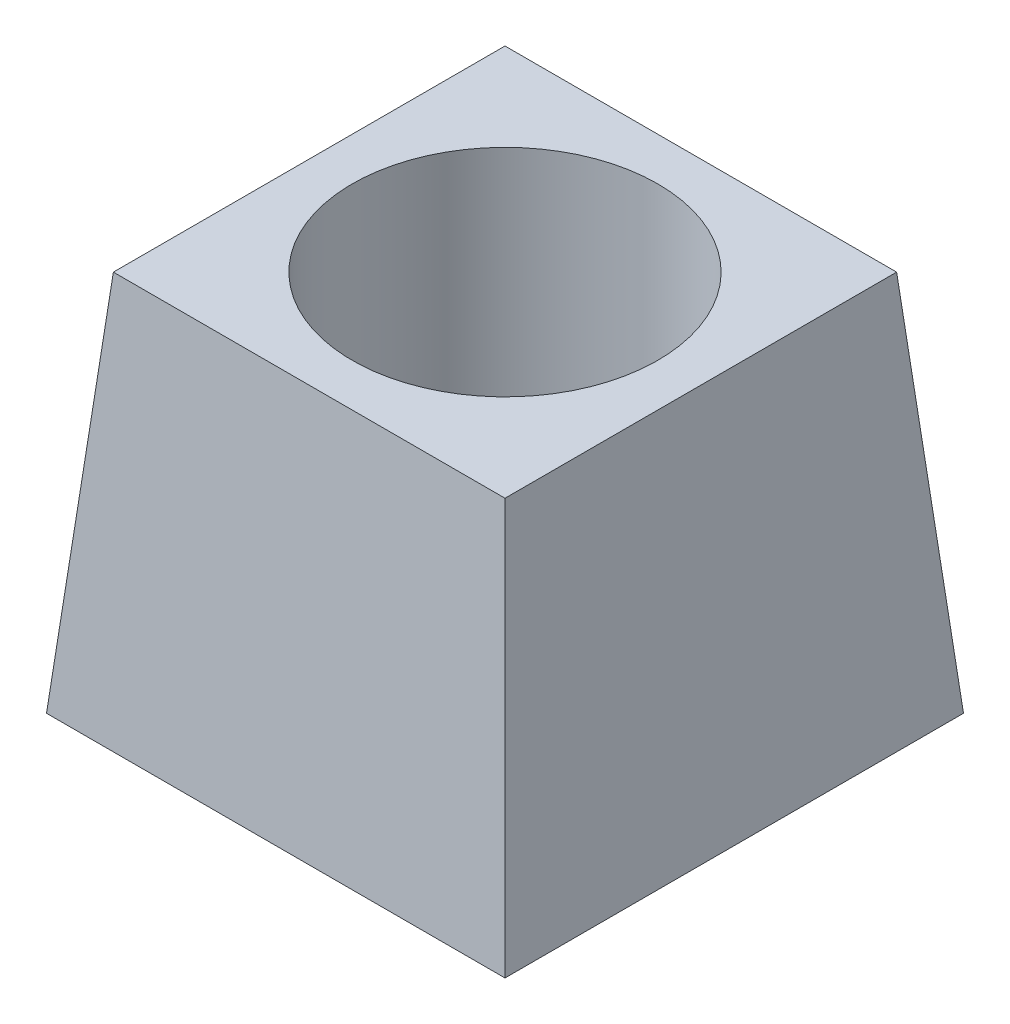
SolidWorks part; units mm, degrees
ref_plane "Plan de face" through (0, 0, 0) normal (0, 0, 1) x (1, 0, 0)
ref_plane "Plan de dessus" through (0, 0, 0) normal (0, 1, 0) x (1, 0, 0)
ref_plane "Plan de droite" through (0, 0, 0) normal (1, 0, 0) x (0, 0, -1)
sketch "Esquisse1" plane through (0, 0, 0) normal (0, 1, 0) x (1, 0, 0)
  line L1 (0, 0) -> (30, 0)
  line L2 (0, 0) -> (0, 30)
  line L3 (0, 30) -> (30, 30)
  line L4 (30, 0) -> (30, 30)
  dimension "D1" = 30
  dimension "D2" = 30
extrude "Extrusion1" add sketch "Esquisse1" along normal blind 25 draft 5
sketch "Esquisse2" plane through (0, 0, 0) normal (0, -1, 0) x (1, 0, 0)
  circle A0 centre (15, -15) radius 10
  dimension "D1" = 20
extrude "Enlèv. mat.-Extru.1" cut sketch "Esquisse2" against normal through all
